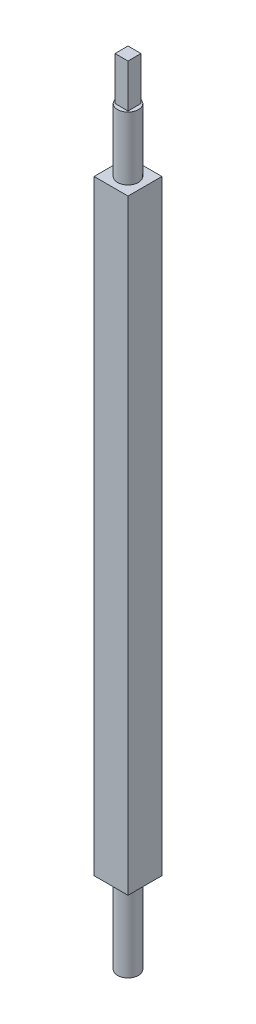
SolidWorks part; units mm, degrees
ref_plane "Front Plane" through (0, 0, 0) normal (0, 0, 1) x (1, 0, 0)
ref_plane "Top Plane" through (0, 0, 0) normal (0, 1, 0) x (1, 0, 0)
ref_plane "Right Plane" through (0, 0, 0) normal (1, 0, 0) x (0, 0, -1)
sketch "Sketch1" plane through (0, 0, 0) normal (0, 1, 0) x (1, 0, 0)
  line L1 (-5.969, 5.969) -> (5.969, 5.969)
  line L2 (-5.969, 5.969) -> (-5.969, -5.969)
  line L3 (-5.969, -5.969) -> (5.969, -5.969)
  line L4 (5.969, 5.969) -> (5.969, -5.969)
  line L9 (-5.969, 5.969) -> (5.969, -5.969) construction
  line L10 (-5.969, -5.969) -> (5.969, 5.969) construction
  point P0 (0, 0)
  dimension "D1" = 11.938
  dimension "D2" = 11.938
extrude "Boss-Extrude1" add sketch "Sketch1" along normal blind 213.106
sketch "Sketch2" plane through (0, 213.106, 0) normal (0, 1, 0) x (1, 0, 0)
  circle A0 centre (0, 0) radius 3.6805
  dimension "D1" = 7.3609
extrude "Boss-Extrude2" add sketch "Sketch2" along normal blind 22.225
sketch "Sketch3" plane through (0, 0, 0) normal (0, -1, 0) x (-1, 0, 0)
  circle A0 centre (0, 0) radius 3.6805
  dimension "D1" = 7.3609
extrude "Boss-Extrude3" add sketch "Sketch3" along normal blind 28.575
sketch "Sketch4" plane through (0, 235.331, 0) normal (0, 1, 0) x (1, 0, 0)
  line L1 (-2.286, 2.286) -> (2.286, 2.286)
  line L2 (-2.286, 2.286) -> (-2.286, -2.286)
  line L3 (-2.286, -2.286) -> (2.286, -2.286)
  line L4 (2.286, 2.286) -> (2.286, -2.286)
  line L5 (-2.286, 2.286) -> (2.286, -2.286) construction
  line L6 (-2.286, -2.286) -> (2.286, 2.286) construction
  point P0 (0, 0)
  dimension "D1" = 4.572
  dimension "D2" = 4.572
extrude "Boss-Extrude4" add sketch "Sketch4" along normal blind 15.24
